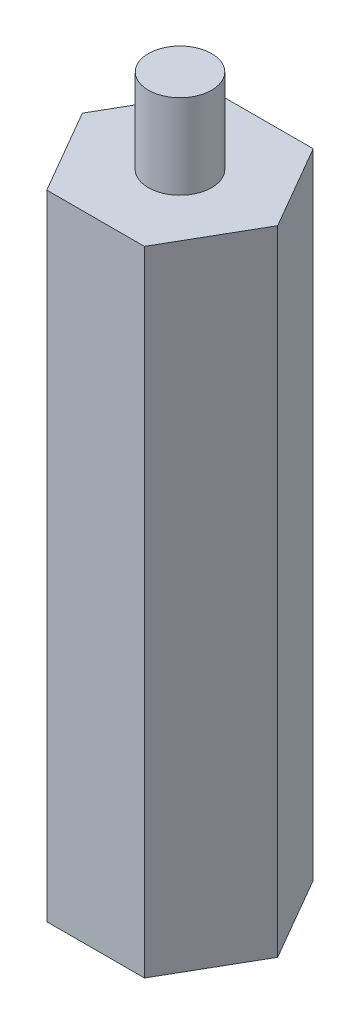
SolidWorks part; units mm, degrees
ref_plane "前视基准面" through (0, 0, 0) normal (0, 0, 1) x (1, 0, 0)
ref_plane "上视基准面" through (0, 0, 0) normal (0, 1, 0) x (1, 0, 0)
ref_plane "右视基准面" through (0, 0, 0) normal (1, 0, 0) x (0, 0, -1)
sketch "草图1" plane through (0, 0, 0) normal (0, 1, 0) x (1, 0, 0)
  line L1 (4.6107, 8.0047) -> (-4.6269, 7.9953)
  line L2 (-4.6269, 7.9953) -> (-9.2376, -0.0094)
  line L3 (-9.2376, -0.0094) -> (-4.6107, -8.0047)
  line L4 (-4.6107, -8.0047) -> (4.6269, -7.9953)
  line L5 (4.6269, -7.9953) -> (9.2376, 0.0094)
  line L6 (9.2376, 0.0094) -> (4.6107, 8.0047)
  circle A0 centre (0, 0) radius 8 construction
extrude "凸台-拉伸1" add sketch "草图1" along normal blind 60
sketch "草图2" plane through (0, 60, 0) normal (0, 1, 0) x (1, 0, 0)
  circle A0 centre (0, 0) radius 3
extrude "凸台-拉伸2" add sketch "草图2" along normal blind 8 contours A0
sketch "草图3" plane through (0, 0, 0) normal (0, -1, 0) x (1, 0, 0)
  circle A0 centre (0, 0) radius 3
extrude "切除-拉伸1" cut sketch "草图3" against normal blind 8
